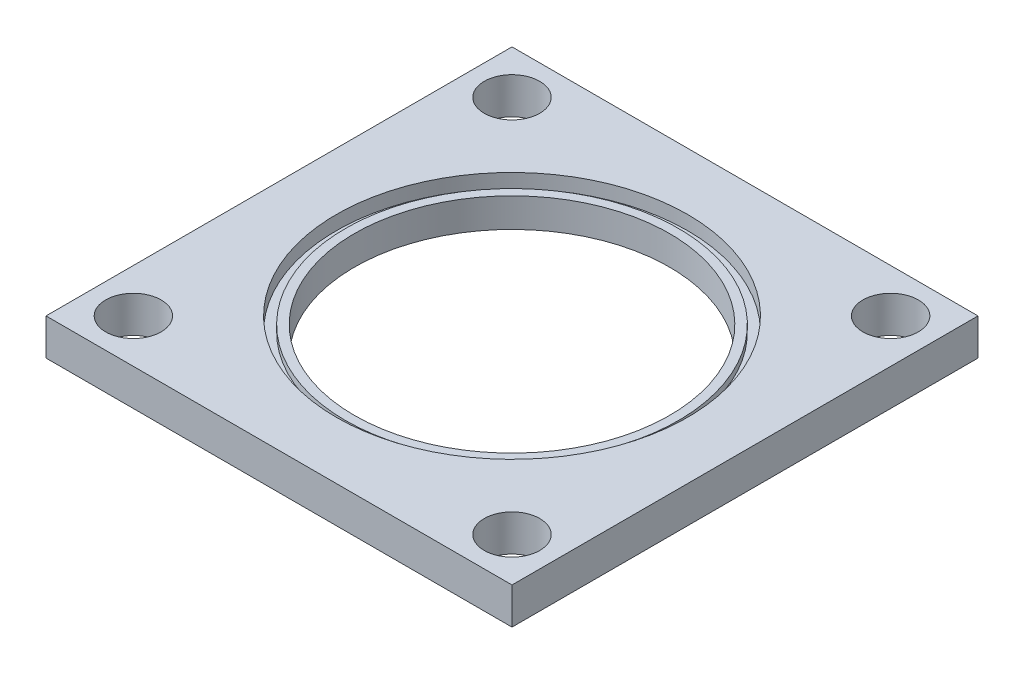
SolidWorks part; units mm, degrees
ref_plane "Front Plane" through (0, 0, 0) normal (0, 0, 1) x (1, 0, 0)
ref_plane "Top Plane" through (0, 0, 0) normal (0, 1, 0) x (1, 0, 0)
ref_plane "Right Plane" through (0, 0, 0) normal (1, 0, 0) x (0, 0, -1)
sketch "plateOutline" plane through (0, 0, 0) normal (0, 1, 0) x (1, 0, 0)
  line L1 (-40, -40) -> (40, -40)
  line L2 (-40, -40) -> (-40, 40)
  line L3 (-40, 40) -> (40, 40)
  line L4 (40, -40) -> (40, 40)
  line L5 (-40, -40) -> (40, 40) construction
  line L6 (-40, 40) -> (40, -40) construction
  line L7 (-40, -40) -> (40, -40) construction
  line L8 (-40, -40) -> (-40, 40) construction
  line L9 (-40, 40) -> (40, 40) construction
  line L10 (40, -40) -> (40, 40) construction
  point P0 (0, 0)
  dimension "D1" = 80
sketch "railGuides" plane through (0, 0, 0) normal (0, 1, 0) x (1, 0, 0)
  line L1 (-32.5, -32.5) -> (32.5, -32.5) construction
  line L2 (-32.5, -32.5) -> (-32.5, 32.5) construction
  line L3 (-32.5, 32.5) -> (32.5, 32.5) construction
  line L4 (32.5, -32.5) -> (32.5, 32.5) construction
  line L6 (-40, 40) -> (-25, 25) construction
  line L7 (40, 40) -> (25, 25) construction
  line L8 (25, -25) -> (40, -40) construction
  line L9 (-40, -40) -> (-25, -25) construction
  line L10 (-40, 40) -> (-25, 25) construction
  circle A0 centre (-32.5, 32.5) radius 4.7625
  circle A1 centre (32.5, 32.5) radius 4.7625
  circle A2 centre (32.5, -32.5) radius 4.7625
  circle A3 centre (-32.5, -32.5) radius 4.7625
sketch "FuelGrainMounting" plane through (0, 0, 0) normal (0, 1, 0) x (1, 0, 0)
  circle A0 centre (0, 0) radius 30.1625
sketch "GasIntake" plane through (0, 0, 0) normal (0, 1, 0) x (1, 0, 0)
  line L0 (-40, 40) -> (40, -40) construction
  circle A0 centre (0, 0) radius 27.051
extrude "Boss-Extrude1" add sketch "plateOutline" along normal blind 6.2738 contours L3 L4 L1 L2
extrude "Cut-Extrude1" cut sketch "railGuides" along normal blind 10
extrude "Cut-Extrude2" cut sketch "FuelGrainMounting" along normal blind 5 from offset 5
extrude "Cut-Extrude3" cut sketch "GasIntake" along normal blind 5
sketch "Sketch1" plane through (0, 0, 0) normal (0, 1, 0) x (1, 0, 0)
  circle A0 centre (0, 0) radius 28.575
  circle A2 centre (0, 0) radius 30.1625
  dimension "D1" = 60.325
  dimension "D2" = 57.15
extrude "Cut-Extrude4" cut sketch "Sketch1" against normal blind 1.143 from offset 5
